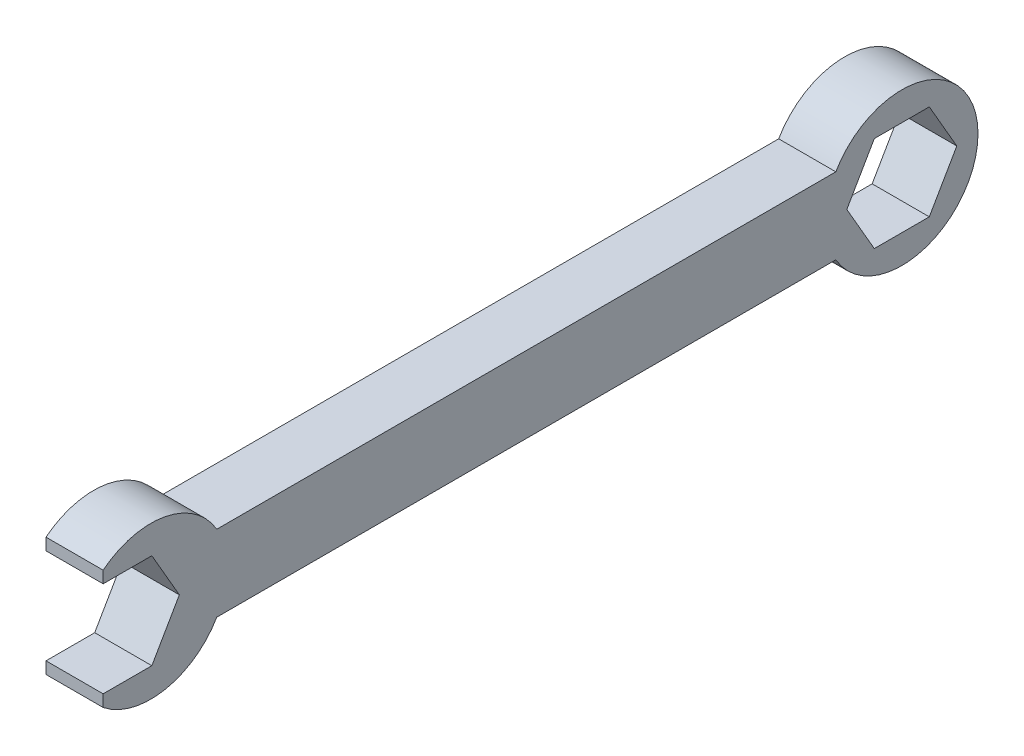
SolidWorks part; units mm, degrees
material "Cast Alloy Steel"
ref_plane "Front Plane" through (0, 0, 0) normal (0, 0, 1) x (1, 0, 0)
ref_plane "Top Plane" through (0, 0, 0) normal (0, 1, 0) x (1, 0, 0)
ref_plane "Right Plane" through (0, 0, 0) normal (1, 0, 0) x (0, 0, -1)
sketch "Sketch1" plane through (0, 0, 0) normal (1, 0, 0) x (0, 0, -1)
  line L0 (0, 0) -> (28081.7428, 0) construction
  line L1 (-41.275, 5.08) -> (41.275, 5.08)
  line L2 (-56.4238, -32.66) -> (-56.4238, 32.66) construction
  line L3 (-41.275, -5.08) -> (41.275, -5.08)
  line L4 (-56.4238, 7.9311) -> (-56.4238, 6.35)
  line L5 (-49.93, 6.35) -> (-56.4238, 6.35)
  line L8 (-56.4238, -6.35) -> (-49.93, -6.35)
  line L9 (-49.93, -6.35) -> (-46.2638, 0)
  line L10 (-46.2638, 0) -> (-49.93, 6.35)
  line L11 (-56.4238, -7.9311) -> (-56.4238, -6.35)
  line L12 (-57.2623, 6.35) -> (-59.0954, 3.175) [skipped]
  line L13 (-59.0954, -3.175) -> (-57.2623, -6.35) [skipped]
  line L15 (57.4062, 0) -> (53.74, 6.35)
  line L16 (53.74, 6.35) -> (46.4076, 6.35)
  line L17 (46.4076, 6.35) -> (42.7415, 0)
  line L18 (42.7415, 0) -> (46.4076, -6.35)
  line L19 (46.4076, -6.35) -> (53.74, -6.35)
  line L20 (53.74, -6.35) -> (57.4062, 0)
  arc A0 (-41.275, 5.08) -> (-56.4238, 7.9311) centre (-50.0738, 0) ccw
  arc A1 (41.275, -5.08) -> (41.275, 5.08) centre (50.0738, 0) ccw
  arc A2 (-41.275, -5.08) -> (-56.4238, -7.9311) centre (-50.0738, 0) cw
  arc A3 (-56.4238, -5.6857) -> (-56.4238, 5.6857) centre (-53.5962, 0) ccw construction
  circle A4 centre (50.0738, 0) radius 6.35 construction
  point P10 (-56.4238, 0)
  point P16 (0, 0)
  dimension "D2" = 5.08
  dimension "D4" = 20.32
  dimension "D1" = 82.55
  dimension "D3" = 6.35
  dimension "D5" = 41.275
  dimension "D6" = 10.16
  dimension "D7" = 12.7
  dimension "D8" = 12.7
extrude "Boss-Extrude1" add sketch "Sketch1" along normal blind 7.62
